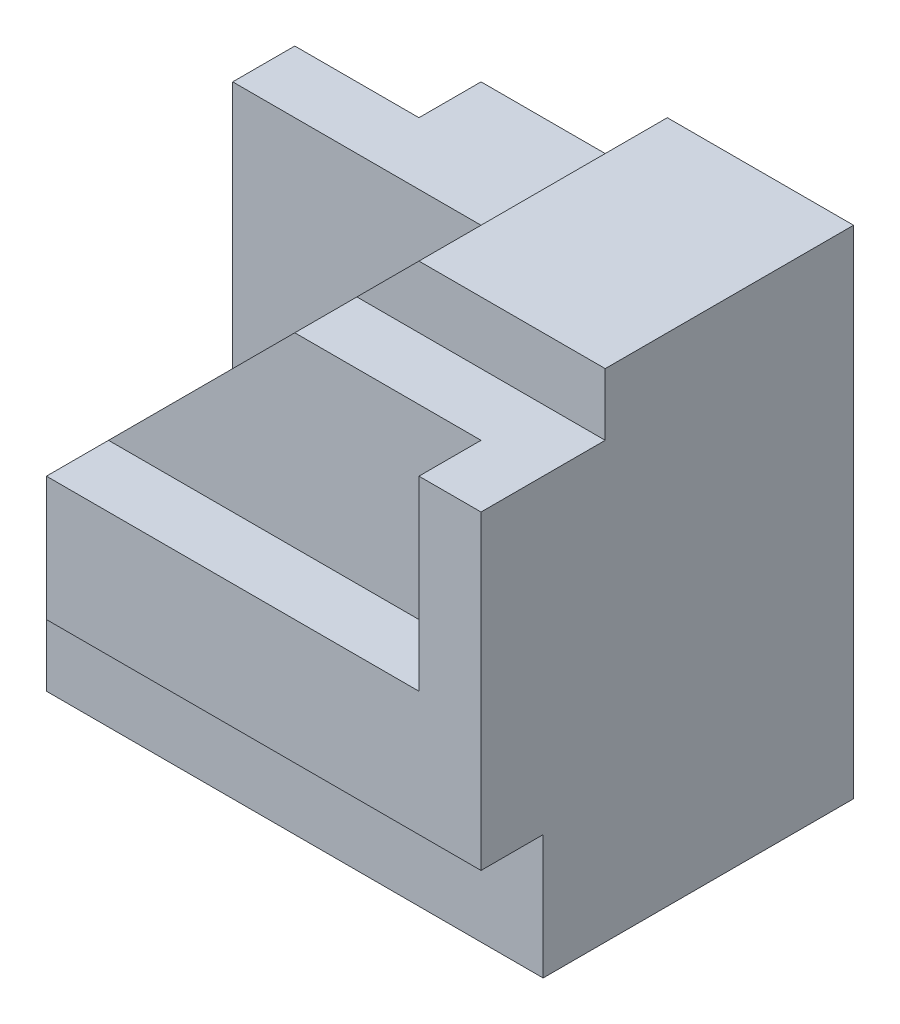
SolidWorks part; units mm, degrees
ref_plane "Front Plane" through (0, 0, 0) normal (0, 0, 1) x (1, 0, 0)
ref_plane "Top Plane" through (0, 0, 0) normal (0, 1, 0) x (1, 0, 0)
ref_plane "Right Plane" through (0, 0, 0) normal (1, 0, 0) x (0, 0, -1)
sketch "Sketch1" plane through (0, 0, 0) normal (0, 1, 0) x (1, 0, 0)
  line L1 (-4, -3) -> (4, -3)
  line L2 (-4, -3) -> (-4, 3)
  line L3 (-4, 3) -> (4, 3)
  line L4 (4, -3) -> (4, 3)
  line L5 (-4, -3) -> (4, 3) construction
  line L6 (-4, 3) -> (4, -3) construction
  point P0 (0, 0)
  dimension "D1" = 6
  dimension "D2" = 8
extrude "Boss-Extrude1" add sketch "Sketch1" along normal blind 8
sketch "Sketch2" plane through (-4, 0, 0) normal (-1, 0, 0) x (0, 0, 1)
  line L1 (3, 0) -> (2, 0)
  line L2 (3, 0) -> (3, 2)
  line L3 (3, 2) -> (2, 2)
  line L4 (2, 0) -> (2, 2)
  dimension "D1" = 1
  dimension "D2" = 2
extrude "Cut-Extrude1" cut sketch "Sketch2" against normal through all
sketch "Sketch3" plane through (0, 0, 3) normal (0, 0, 1) x (1, 0, 0)
  line L0 (-4, 8) -> (4, 8) construction
  line L1 (3, 8) -> (-4, 8)
  line L2 (3, 8) -> (3, 4)
  line L3 (3, 4) -> (-4, 4)
  line L4 (-4, 8) -> (-4, 4)
  line L5 (-4, 8) -> (-4, 2) construction
  line L6 (4, 8) -> (4, 2) construction
  dimension "D1" = 4
  dimension "D2" = 1
extrude "Cut-Extrude2" cut sketch "Sketch3" against normal blind 1
sketch "Sketch4" plane through (0, 0, 3) normal (0, 0, 1) x (1, 0, 0)
  line L1 (4, 8) -> (1, 8)
  line L2 (4, 8) -> (4, 7)
  line L3 (4, 7) -> (1, 7)
  line L4 (1, 8) -> (1, 7)
  dimension "D1" = 3
  dimension "D2" = 1
extrude "Cut-Extrude3" cut sketch "Sketch4" against normal blind 2
sketch "Sketch5" plane through (0, 0, 2) normal (0, 0, 1) x (1, 0, 0)
  line L0 (1, 8) -> (-3, 4)
  line L1 (-4, 4) -> (3, 4) construction
  line L2 (-4, 8) -> (1, 8)
  line L3 (-3, 4) -> (-4, 4)
  line L4 (-4, 4) -> (-4, 8)
  dimension "D1" = 4
extrude "Cut-Extrude4" cut sketch "Sketch5" against normal blind 3
sketch "Sketch8" plane through (1, 0, 0) normal (1, 0, 0) x (0, 0, -1)
  line L1 (-2, 8) -> (-1, 8)
  line L2 (-2, 8) -> (-2, 7)
  line L3 (-2, 7) -> (-1, 7)
  line L4 (-1, 8) -> (-1, 7)
extrude "Cut-Extrude7" cut sketch "Sketch8" against normal blind 1
sketch "Sketch9" plane through (0, 0, -1) normal (0, 0, 1) x (1, 0, 0)
  line L0 (1, 8) -> (-4, 8) construction
  line L1 (0, 8) -> (1, 8)
  line L2 (0, 8) -> (0, 7)
  line L5 (0, 7) -> (1, 8)
  point P0 (0, 8)
  dimension "D1" = 1
extrude "Cut-Extrude8" cut sketch "Sketch9" against normal through all
sketch "Sketch10" plane through (0, 8, 0) normal (0, 1, 0) x (1, 0, 0)
  line L0 (-4, 1) -> (-4, 2)
  line L1 (-4, 3) -> (-4, 1) construction
  line L2 (-4, 2) -> (-2, 2)
  line L3 (-2, 2) -> (-2, 3)
  line L4 (0, 3) -> (-4, 3) construction
  line L5 (-2, 3) -> (0, 3)
  line L6 (0, 3) -> (0, 1)
  line L7 (0, 1) -> (-4, 1)
  dimension "D1" = 1
  dimension "D2" = 2
extrude "Cut-Extrude9" cut sketch "Sketch10" against normal blind 1
sketch "Sketch14" plane through (-4, 0, 0) normal (-1, 0, 0) x (0, 0, 1)
  line L1 (3, 2) -> (-1, 2)
  line L2 (3, 2) -> (3, 4)
  line L3 (3, 4) -> (-1, 4)
  line L4 (-1, 2) -> (-1, 4)
extrude "Cut-Extrude12" cut sketch "Sketch14" against normal blind 1
sketch "Sketch15" plane through (-4, 0, 0) normal (-1, 0, 0) x (0, 0, 1)
  line L0 (-3, 8) -> (-2, 8)
  line L1 (-2, 8) -> (-2, 7)
  line L2 (-2, 7) -> (-1, 7)
  line L3 (-1, 7) -> (-1, 2)
  line L4 (-1, 2) -> (0, 2)
  line L5 (-1, 2) -> (2, 2) construction
  line L6 (0, 2) -> (0, 0)
  line L7 (0, 0) -> (-3, 0)
  line L8 (-3, 0) -> (-3, 8)
extrude "Boss-Extrude2" add sketch "Sketch15" along normal blind 1
sketch "Sketch16" plane through (0, 7, 0) normal (0, 1, 0) x (1, 0, 0)
  line L0 (-5, 1) -> (0, 1) construction
  line L1 (-5, 2) -> (-4, 2)
  line L2 (-5, 2) -> (-5, 1)
  line L3 (-5, 1) -> (-4, 1)
  line L4 (-4, 2) -> (-4, 1)
  dimension "D1" = 1
extrude "Cut-Extrude13" cut sketch "Sketch16" against normal blind 5
sketch "Sketch17" plane through (0, 0, -3) normal (0, 0, -1) x (-1, 0, 0)
  line L0 (2, 7) -> (5, 4)
  line L1 (5, 8) -> (5, 0) construction
  line L2 (5, 4) -> (5, 8)
  line L3 (5, 8) -> (2, 8)
  line L4 (2, 8) -> (2, 7)
  dimension "D1" = 3
extrude "Cut-Extrude14" cut sketch "Sketch17" against normal blind 1
